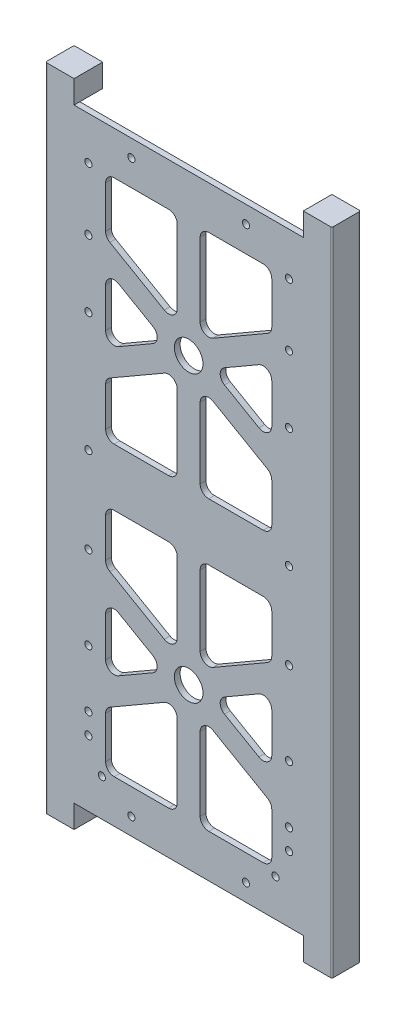
SolidWorks part; units mm, degrees
material "6061-T6 (SS)"
ref_plane "Front Plane" through (0, 0, 0) normal (0, 0, 1) x (1, 0, 0)
ref_plane "Top Plane" through (0, 0, 0) normal (0, 1, 0) x (1, 0, 0)
ref_plane "Right Plane" through (0, 0, 0) normal (1, 0, 0) x (0, 0, -1)
sketch "Sketch1" plane through (0, 0, 0) normal (0, 0, 1) x (1, 0, 0)
  line L1 (0, 0) -> (88, 0)
  line L2 (0, 0) -> (0, 211)
  line L3 (0, 211) -> (88, 211)
  line L4 (88, 0) -> (88, 211)
  dimension "D1" = 88
  dimension "D2" = 211
extrude "Boss-Extrude1" add sketch "Sketch1" along normal blind 2
sketch "Sketch2" plane through (0, 0, 2) normal (0, 0, 1) x (1, 0, 0)
  line L0 (0, 105.5) -> (88, 105.5) construction
  line L1 (0, 211) -> (0, 0) construction
  line L2 (88, 0) -> (88, 211) construction
  line L3 (44, 211) -> (44, 0) construction
  line L4 (88, 211) -> (0, 211) construction
  line L5 (0, 0) -> (88, 0) construction
  line L6 (0, 155.25) -> (88, 155.25) construction
  line L7 (0, 55.75) -> (88, 55.75) construction
  dimension "D1" = 55.75
  dimension "D2" = 55.75
sketch "Sketch3" plane through (0, 0, 2) normal (0, 0, 1) x (1, 0, 0)
  line L0 (0, 155.25) -> (88, 155.25) construction
  line L2 (0, 211) -> (0, 0) construction
  line L3 (15, 196) -> (73, 196)
  line L4 (15, 196) -> (15, 115.5)
  line L5 (15, 115.5) -> (73, 115.5)
  line L6 (73, 196) -> (73, 115.5)
  line L7 (88, 211) -> (0, 211) construction
  line L8 (88, 0) -> (88, 211) construction
  line L9 (0, 105.5) -> (88, 105.5) construction
  line L10 (40, 196) -> (40, 115.5)
  line L11 (48, 196) -> (48, 115.5)
  line L12 (44, 211) -> (44, 0) construction
  line L13 (73, 171.9932) -> (15, 138.5068) construction
  line L14 (15, 171.9932) -> (73, 138.5068) construction
  line L15 (73, 176.612) -> (15, 143.1256)
  line L16 (73, 167.3744) -> (15, 133.888)
  line L17 (15, 176.612) -> (73, 143.1256)
  line L18 (15, 167.3744) -> (73, 133.888)
  circle A0 centre (44, 155.25) radius 5
  dimension "D1" = 10
  dimension "D3" = 15
  dimension "D4" = 15
  dimension "D5" = 15
  dimension "D6" = 10
  dimension "D7" = 8
  dimension "D8" = 4
  dimension "D9" = 30
  dimension "D10" = 30
  dimension "D11" = 8
  dimension "D12" = 4
  dimension "D13" = 4
  dimension "D14" = 8
ref_plane "Plane1" through (0, 105.5, 0) normal (0, -1, 0) x (1, 0, 0)
extrude "Cut-Extrude2" cut sketch "Sketch3" against normal blind 2 contours L18 L11 L5 L6 | L10 L16 L4 L5 | L18 L4 L15 | L16 L17 L6 | L15 L6 L3 L11 | L4 L17 L10 L3
sketch "Sketch4" plane through (0, 0, 2) normal (0, 0, 1) x (1, 0, 0)
  line L0 (0, 155.25) -> (88, 155.25) construction
  circle A0 centre (44, 155.25) radius 5
  dimension "D1" = 10
extrude "Cut-Extrude3" cut sketch "Sketch4" against normal through all
mirror "Mirror2" about plane through (0, 105.5, 0) normal (0, -1, 0) of "Cut-Extrude3", "Cut-Extrude2"
fillet "Fillet2" radius 3 44 edges at (73, 67.8744, 1) (73, 43.6256, 1) (52, 55.75, 1) (40, 48.8218, 1) (40, 15, 1) (15, 15, 1) (15, 34.388, 1) (15, 143.1256, 1) (15, 167.3744, 1) (36, 155.25, 1) (15, 115.5, 1) (15, 133.888, 1) (40, 148.3218, 1) (40, 115.5, 1) (48, 196, 1) (73, 196, 1) (48, 162.1782, 1) (73, 115.5, 1) (48, 115.5, 1) (48, 148.3218, 1) (73, 133.888, 1) (15, 196, 1) (40, 196, 1) (40, 162.1782, 1) (15, 176.612, 1) (73, 167.3744, 1) (73, 143.1256, 1) (52, 155.25, 1) (48, 62.6782, 1) (48, 95.5, 1) (73, 95.5, 1) (73, 77.112, 1) (73, 34.388, 1) (73, 15, 1) (48, 15, 1) (48, 48.8218, 1) (40, 62.6782, 1) (15, 77.112, 1) (15, 95.5, 1) (40, 95.5, 1) (15, 43.6256, 1) (15, 67.8744, 1) (36, 55.75, 1) (73, 176.612, 1)
sketch "Sketch5" plane through (0, 0, 2) normal (0, 0, 1) x (1, 0, 0)
  line L0 (88, 0) -> (88, 211) construction
  line L1 (0, 211) -> (0, 0) construction
  line L4 (0, 5.5) -> (88, 5.5) construction
  line L5 (0, 0) -> (88, 0) construction
  line L6 (0, 205.5) -> (88, 205.5) construction
  circle A1 centre (64, 205.5) radius 1.5
  circle A3 centre (64, 5.5) radius 1.5
  circle A4 centre (24, 5.5) radius 1.5
  circle A5 centre (24, 205.5) radius 1.5
  dimension "D5" = 3
  dimension "D2" = 40
  dimension "D3" = 24
  dimension "D1" = 200
  dimension "D4" = 5.5
  dimension "D6" = 3
  dimension "D7" = 40
  dimension "D8" = 24
  dimension "D9" = 3
  dimension "D10" = 24
  dimension "D11" = 24
  dimension "D12" = 3
sketch "Sketch7" plane through (0, 0, 2) normal (0, 0, 1) x (1, 0, 0)
  line L0 (0, 105.5) -> (151.3859, 105.5) construction
  line L5 (0, 211) -> (0, 0) construction
  line L7 (44, 211) -> (44, 0) construction
  line L8 (88, 211) -> (0, 211) construction
  line L9 (0, 0) -> (88, 0) construction
  line L17 (94, 219) -> (84, 219)
  line L53 (88, 0) -> (88, 211)
  line L54 (84, 219) -> (84, 211)
  line L55 (84, 0) -> (88, 0)
  line L56 (94, 0) -> (94, 211)
  line L57 (94, -8) -> (94, 219)
  line L58 (88, 211) -> (0, 211) construction
  line L59 (84, 211) -> (88, 211)
  line L60 (84, -8) -> (84, 0)
  line L61 (94, -8) -> (84, -8)
  line L62 (-6, -8) -> (4, -8)
  line L63 (4, -8) -> (4, 0)
  line L64 (4, 0) -> (0, 0)
  line L65 (0, 0) -> (0, 211)
  line L66 (4, 211) -> (0, 211)
  line L67 (4, 219) -> (4, 211)
  line L68 (-6, 219) -> (4, 219)
  line L69 (-6, -8) -> (-6, 219)
  dimension "D1" = 6
extrude "Boss-Extrude2" add sketch "Sketch7" against normal blind 10
sketch "Sketch53" plane through (0, 0, -8) normal (0, 0, -1) x (-1, 0, 0)
  line L0 (-84, 0) -> (-84, 211)
  line L1 (-84, 211) -> (-90, 211)
  line L2 (-92, 209) -> (-92, 2)
  line L4 (-44, 0) -> (-44, 211)
  line L5 (-4, 0) -> (-84, 0) construction
  line L6 (-84, 211) -> (-4, 211) construction
  line L8 (-90, 0) -> (-84, 0)
  line L9 (4, 209) -> (4, 2)
  line L10 (-4, 211) -> (2, 211)
  line L11 (-4, 0) -> (-4, 211)
  line L12 (2, 0) -> (-4, 0)
  arc A0 (-92, 209) -> (-90, 211) centre (-90, 209) cw
  arc A1 (-90, 0) -> (-92, 2) centre (-90, 2) cw
  arc A2 (4, 209) -> (2, 211) centre (2, 209) ccw
  arc A3 (2, 0) -> (4, 2) centre (2, 2) ccw
  line M9 (-88, 0) -> (-88, 211)
  dimension "D1" = 2
  dimension "D2" = 2
extrude "Cut-Extrude5" cut sketch "Sketch53" against normal blind 8 contours A1 L8 L1 A0 L2 M9 | L12 A3 L9 A2 L10 L11
hole_wizard "M3x0.5 Tapped Hole1" positions "Sketch55" profile "Sketch56" tap size "M3x0.5" standard "ANSI Metric"
sketch "Sketch55" plane through (0, 0, 2) normal (0, 0, 1) x (1, 0, 0)
  line L0 (-6, 219) -> (-6, -8) construction
  line L1 (84, 211) -> (4, 211) construction
  line L3 (44, 211) -> (44, 0) construction
  line L4 (4, 0) -> (84, 0) construction
  line L5 (4, 0) -> (84, 0) construction
  line L6 (9, 30.2) -> (9, 211) construction
  point P0 (9, 174.3)
  point P2 (9, 150.9)
  point P4 (9, 109.2)
  point P6 (9, 79.2)
  point P8 (9, 50.2)
  point P10 (9, 30.2)
  point P25 (13.7, 13)
  point P40 (24, 205)
  point P42 (24, 6)
  point P44 (9, 23)
  point P47 (9, 196)
  dimension "D2" = 36.7
  dimension "D3" = 23.4
  dimension "D4" = 101.8
  dimension "D5" = 20
  dimension "D6" = 29
  dimension "D7" = 30
  dimension "D8" = 15
  dimension "D9" = 23
  dimension "D10" = 20
  dimension "D11" = 6
  dimension "D12" = 19.7
  dimension "D13" = 13
  dimension "D14" = 35
  dimension "D15" = 6
sketch "Sketch56" plane through (9, 174.3, 2) normal (1, 0, 0) x (0, -1, 0)
  line L0 (0, 0) -> (0, 10.7511)
  line L1 (0, 10.7511) -> (1.25, 10)
  line L2 (1.25, 10) -> (1.25, 0)
  line L5 (1.25, 0) -> (0, 0)
  line L10 (0, 10.7511) -> (-1.25, 10) construction
  line L11 (0, -6.35) -> (0, 107.95) construction
  dimension "Tap Drill Dia." = 2.5
  dimension "Tap Drill Depth" = 10
  dimension "Drill Angle" = 118
ref_plane "Plane2" through (44, 0, 0) normal (-1, 0, 0) x (0, 0, 1)
mirror "Mirror3" about plane through (44, 0, 0) normal (-1, 0, 0) of "M3x0.5 Tapped Hole1"
ref_plane "Plane3" through (44, 0, 0) normal (1, 0, 0) x (0, 0, -1)
sketch "Sketch58" plane through (0, 0, 0) normal (0, 0, -1) x (-1, 0, 0)
  line L0 (-13.7, 13) -> (6, 13) construction
  line L1 (6, 219) -> (6, -8) construction
  line L2 (-14.95, 13) -> (-12.45, 13) construction
  line L3 (-13.7, 11.75) -> (-13.7, 14.25) construction
  circle A0 centre (-0.7, 13) radius 1.665
  circle A1 centre (-13.7, 13) radius 1.25 construction
  point P9 (-13.7, 13)
  dimension "D1" = 3.33
  dimension "D2" = 13
extrude "Cut-Extrude9" cut sketch "Sketch58" against normal blind 1.8 contours A0
mirror "Mirror4" about plane through (44, 0, 0) normal (1, 0, 0) of "Cut-Extrude9"
sketch "Sketch59" plane through (0, -8, 0) normal (0, -1, 0) x (-1, 0, 0)
  line L0 (-94, 8) -> (-94, -2) construction
  line L1 (6, 8) -> (6, -2) construction
  line L2 (-84, 8) -> (-94, 8) construction
  circle A0 centre (-89, 2.4) radius 2
  circle A1 centre (1, 2.4) radius 2
  dimension "D1" = 4
  dimension "D2" = 5
  dimension "D3" = 5
  dimension "D4" = 5.6
extrude "Cut-Extrude10" cut sketch "Sketch59" against normal blind 10
fillet "Fillet3" radius 0.5 4 edges at (-6, 105.5, 2) (-6, 105.5, -8) (94, 105.5, -8) (94, 105.5, 2)
